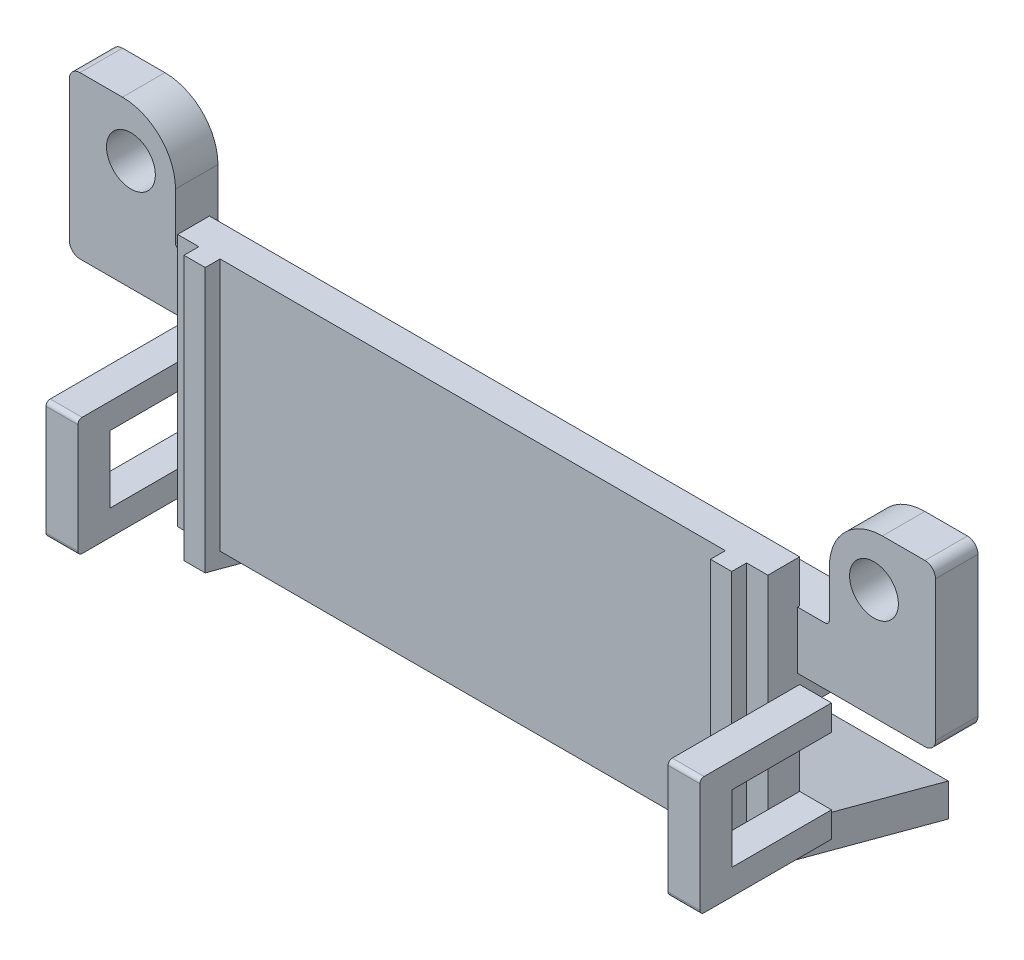
SolidWorks part; units mm, degrees
ref_plane "前视基准面" through (0, 0, 0) normal (0, 0, 1) x (1, 0, 0)
ref_plane "上视基准面" through (0, 0, 0) normal (0, 1, 0) x (1, 0, 0)
ref_plane "右视基准面" through (0, 0, 0) normal (1, 0, 0) x (0, 0, -1)
sketch "草图1" plane through (0, 0, 0) normal (0, 0, 1) x (1, 0, 0)
  line L0 (0, 0) -> (27.8, 0)
  line L1 (27.8, 0) -> (27.8, -8)
  line L2 (27.8, -8) -> (0, -8)
  line L3 (0, -8) -> (0, 0)
  line L4 (0, 0) -> (0.194, -0.0613)
  dimension "D1" = 27.8
  dimension "D2" = 8
extrude "凸台-拉伸1" add sketch "草图1" along normal blind 7.8
sketch "草图2" plane through (0, 0, 0) normal (-1, 0, 0) x (0, 0, 1)
  line L0 (5.7956, -15.9471) -> (0, -17.5)
  line L1 (0, -8) -> (0, -17.5)
  line L2 (7.8, -8) -> (5.7956, -15.9471)
  line L3 (0, -8) -> (7.8, -8)
  dimension "D1" = 75
  dimension "D2" = 9.5
  dimension "D3" = 6
extrude "凸台-拉伸2" add sketch "草图2" against normal up to surface (27.8 mm away) up to face at (27.8, -4, 3.9)
ref_plane "基准面1" through (0, 0, -1.9) normal (0, 0, -1) x (-1, 0, 0)
sketch "草图4" plane through (0, 0, -1.9) normal (0, 0, -1) x (-1, 0, 0)
  line L0 (0, 0) -> (0, -2) construction
  line L1 (0, -2) -> (5.3571, -2) construction
  line L3 (5.3571, 0) -> (0, 0) construction
  line L4 (0, -2) -> (0, -4.7)
  line L5 (0, -4.7) -> (6, -4.7)
  line L6 (6.5, -4.2) -> (6.5, -2)
  line L7 (1.3, -2) -> (0, -2)
  line L8 (1.5, -1.8) -> (1.5, 0.4)
  line L9 (4, 2.9) -> (6, 2.9)
  line L10 (6.5, 2.4) -> (6.5, -2)
  line L11 (0, 0) -> (-27.8, 0) construction
  arc A0 (1.5, 0.4) -> (4, 2.9) centre (4, 0.4) cw
  circle A1 centre (3.6, 0.5) radius 1.15
  arc A2 (6, 2.9) -> (6.5, 2.4) centre (6, 2.4) cw
  arc A3 (1.5, -1.8) -> (1.3, -2) centre (1.3, -1.8) cw
  arc A4 (6, -4.7) -> (6.5, -4.2) centre (6, -4.2) ccw
  dimension "D1" = 3.6
  dimension "D7" = 2.5
  dimension "D8" = 0.5
  dimension "D9" = 0.5
  dimension "D2" = 5.2
  dimension "D5" = 7.6
  dimension "D10" = 2.3
  dimension "D11" = 0.2
  dimension "D3" = 1.5
  dimension "D4" = 2
  dimension "D6" = 2.7
extrude "凸台-拉伸3" add sketch "草图4" against normal blind 2
ref_plane "基准面3" through (1.5, 0, 0) normal (-1, 0, 0) x (0, 0, 1)
ref_plane "基准面2" through (13.9, 0, 0) normal (-1, 0, 0) x (0, 0, 1)
mirror "镜向1" about plane through (13.9, 0, 0) normal (-1, 0, 0) of "凸台-拉伸3"
sketch "草图13" plane through (1.5, 0, 0) normal (-1, 0, 0) x (0, 0, 1)
  line L0 (1.5, 0) -> (1.5, -11.9217)
  line L1 (4.5565, -14.7262) -> (6.3, -7.8137)
  line L2 (1.5, 0) -> (6.3, 0)
  line L3 (6.3, 0) -> (6.3, -7.8137)
  line L4 (7.8, -8) -> (7.8, 0) construction
  line L5 (0, -17.5) -> (0, -4.7) construction
  line L6 (4.5565, -14.7262) -> (0, -15.9471)
  line L7 (1.5, -11.9217) -> (0, -12.3236)
  line L8 (0, -12.3236) -> (0, -15.9471)
  line L9 (0, -17.5) -> (5.7956, -15.9471) construction
  line L10 (7.8, 0) -> (0, 0) construction
  line L11 (5.7956, -15.9471) -> (7.8, -8) construction
  dimension "D1" = 1.5
  dimension "D5" = 1.5
  dimension "D2" = 1.5
  dimension "D3" = 1.5
  dimension "D4" = 3.5
extrude "切除-拉伸4" cut sketch "草图13" against normal blind 24.8
sketch "草图14" [suppressed] plane through (0, 0, 0) normal (0, 0, -1) x (-1, 0, 0)
  line L0 (-27.8, -1.5) -> (0, -1.5)
  line L1 (0, -1.5) -> (0, -3.5)
  line L2 (0, -17.5) -> (0, -4.7) construction
  line L3 (0, -3.5) -> (-27.8, -3.5)
  line L4 (-27.8, -1.5) -> (-27.8, -2) construction
  line L5 (-27.8, -3.5) -> (-27.8, -1.5)
  dimension "D1" = 2
extrude "切除-拉伸5" [suppressed] cut sketch "草图14" against normal blind 10
sketch "草图15" plane through (0, 0, 0) normal (0, 0, -1) x (-1, 0, 0)
  line L0 (-27.8, -2) -> (0, -2)
  line L1 (0, -2) -> (0, -6.2518)
  line L2 (0, -17.5) -> (0, -4.7) construction
  line L3 (0, -6.2518) -> (-27.8, -6.2518)
  line L4 (-27.8, -4.7) -> (-27.8, -17.5) construction
  line L5 (-27.8, -6.2518) -> (-27.8, -2)
extrude "凸台-拉伸4" add sketch "草图15" along normal up to surface (1.9 mm away) up to face at (31.1031, -1.0324, -1.9)
chamfer "倒角1" [suppressed] distance 1.9 angle 45
ref_plane "基准面4" through (13.9, 0, 0) normal (-1, 0, 0) x (0, 0, 1)
sketch "草图16" plane through (13.9, 0, 0) normal (-1, 0, 0) x (0, 0, 1)
  line L0 (4.5565, -14.7262) -> (-32.5836, -24.6778) construction
  line L1 (0, -15.9471) -> (4.5565, -14.7262) construction
  line L2 (-32.5495, -21.0452) -> (1.5, -11.9217) construction
  line L3 (1.5, -11.9217) -> (0, -12.3236) construction
fillet "圆角1" radius 8 1 edges at (13.9, -14.7262, 4.5565)
fillet "圆角2" radius 6.5 1 edges at (13.9, -15.9471, 5.7956)
sketch "草图17" plane through (27.8, 0, 0) normal (1, 0, 0) x (0, 0, -1)
  line L0 (0, -17.5) -> (7, -19.3756)
  line L1 (7, -19.3756) -> (7, -12.6463)
  line L2 (7, -12.6463) -> (0, -10.7707)
  line L3 (0, -6.2518) -> (0, -17.5) construction
  line L4 (0, -10.7707) -> (0, -17.5)
  line L5 (0, -17.5) -> (-2.1087, -16.935) construction
  line L7 (-1.5, -11.9217) -> (0, -12.3236) construction
  dimension "D1" = 7
  dimension "D2" = 1.5
extrude "凸台-拉伸5" add sketch "草图17" against normal up to surface (27.8 mm away) up to face at (0, -6.7677, 1.7896)
sketch "草图18" plane through (26.3, 0, 0) normal (-1, 0, 0) x (0, 0, 1)
  line L0 (0, -12.3236) -> (0, -15.9471)
  line L1 (0, -15.9471) -> (-7, -17.8227)
  line L2 (-7, -17.8227) -> (-7, -14.1993)
  line L3 (-7, -14.1993) -> (0, -12.3236)
  line L4 (-7, -19.3756) -> (2.1087, -16.935) construction
  line L5 (-7, -19.3756) -> (-7, -12.6463) construction
extrude "切除-拉伸6" cut sketch "草图18" along normal up to surface (24.8 mm away) up to face at (1.5, -9.3615, 2.7636)
sketch "草图19" plane through (34.3, 0, 0) normal (1, 0, 0) x (0, 0, -1)
  line L0 (7, 2.9) -> (7, -14.1993)
  line L1 (7, -19.3756) -> (7, -12.6463) construction
  line L2 (7, -14.1993) -> (-1.5, -11.9217)
  line L3 (-1.5, -11.9217) -> (-1.5, 2.9)
  line L5 (-1.5, -11.9217) -> (7, -14.1993) construction
  line L6 (-1.5, 2.9) -> (7, 2.9)
  line L7 (-1.5, 0) -> (-1.5, -11.9217) construction
  line L9 (-0.1, 2.9) -> (1.9, 2.9) construction
extrude "切除-拉伸7" cut sketch "草图19" against normal up to surface (40.8 mm away) flip side to cut up to face at (-6.5, -0.9, -0.9)
sketch "草图20" plane through (0, -7.983, 0) normal (0, 0, -1) x (1, 0, 0)
  line L0 (0, 2.7877) -> (-1.5, 2.7877)
  line L1 (-1.5, 2.7877) -> (-1.5, -2.7723)
  line L2 (-1.5, -2.7723) -> (0, -2.7723)
  line L3 (0, -2.7723) -> (0, 2.7877)
  dimension "D1" = 1.5
  dimension "D2" = 5.56
extrude "凸台-拉伸6" add sketch "草图20" against normal blind 6.2
sketch "草图21" plane through (0, -7.983, 0) normal (0, 0, -1) x (1, 0, 0)
  line L0 (-1.5, 1.5877) -> (-1.5, -1.5723)
  line L1 (-1.5, 2.7877) -> (-1.5, -2.7723) construction
  line L2 (-1.5, -1.5723) -> (0, -1.5723)
  line L3 (0, -1.5723) -> (0, 1.5877)
  line L4 (0, 1.5877) -> (-1.5, 1.5877)
  line L7 (0, 2.7877) -> (-1.5, 2.7877) construction
  dimension "D1" = 1.5
  dimension "D2" = 3.16
  dimension "D3" = 1.2
extrude "切除-拉伸8" cut sketch "草图21" against normal blind 4.68
ref_plane "基准面5" through (13.9, 0, 0) normal (-1, 0, 0) x (0, 0, 1)
mirror "镜向2" about plane through (13.9, 0, 0) normal (-1, 0, 0) of "切除-拉伸8", "凸台-拉伸6"
ref_plane "基准面6" through (1, 0, 0) normal (-1, 0, 0) x (0, 0, 1)
sketch "草图23" plane through (1, 0, 0) normal (-1, 0, 0) x (0, 0, 1)
  line L0 (1.5, 0) -> (1.5, -11.9217)
  line L1 (-7, -14.1993) -> (1.5, -11.9217) construction
  line L2 (2.2, -12.4588) -> (2.2, 0)
  line L3 (2.2, 0) -> (1.5, 0)
  line L4 (1.5, 0) -> (0, 0) construction
  line L6 (1.5, -11.9217) -> (-7, -14.1993)
  line L7 (-7, -14.1993) -> (-7, -14.924)
  line L8 (-7, -14.924) -> (2.2, -12.4588)
  line L9 (-7, -14.1993) -> (-7, -12.6463) construction
  dimension "D1" = 0.7
  dimension "D2" = 0.7
extrude "凸台-拉伸7" add sketch "草图23" against normal blind 1
ref_plane "基准面7" through (13.9, 0, 0) normal (-1, 0, 0) x (0, 0, 1)
mirror "镜向3" about plane through (13.9, 0, 0) normal (-1, 0, 0) of "凸台-拉伸7"
fillet "圆角3" radius 0.2 4 edges at (28.55, -10.7707, 6.2) (28.55, -5.2107, 6.2) (-0.75, -10.7707, 6.2) (-0.75, -5.2107, 6.2)
